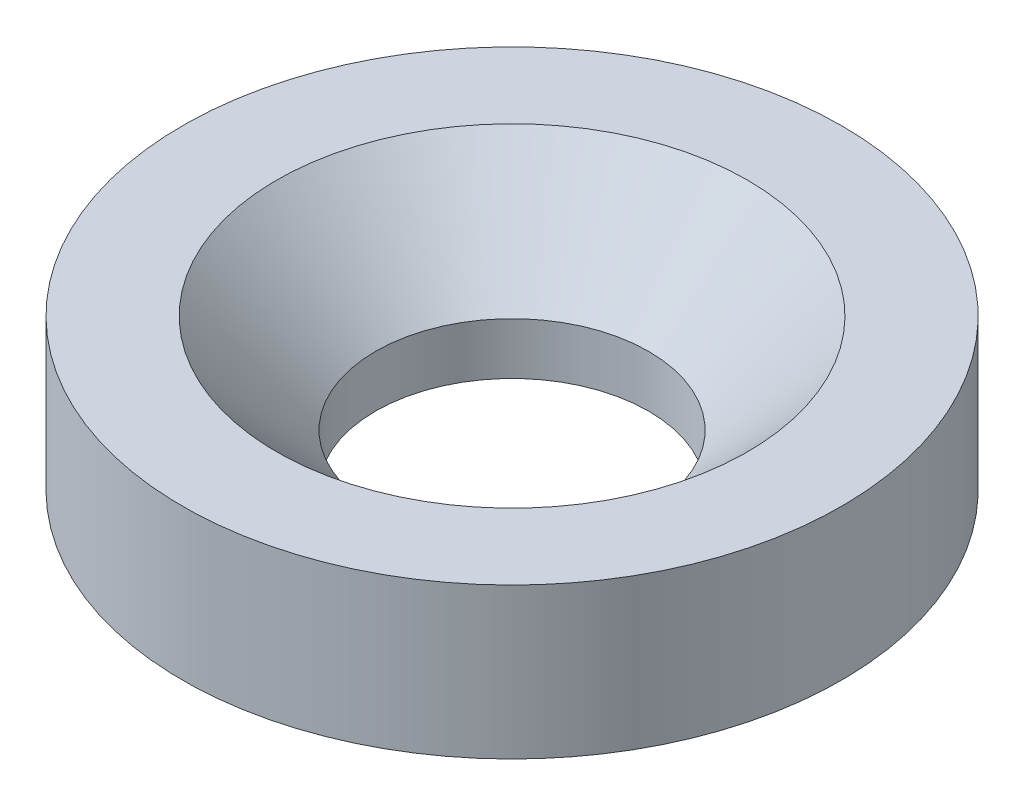
SolidWorks part; units mm, degrees
material "AISI 1020"
ref_plane "Front Plane" through (0, 0, 0) normal (0, 0, 1) x (1, 0, 0)
ref_plane "Top Plane" through (0, 0, 0) normal (0, 1, 0) x (1, 0, 0)
ref_plane "Right Plane" through (0, 0, 0) normal (1, 0, 0) x (0, 0, -1)
sketch "Sketch1" plane through (0, 0, 0) normal (0, 0, 1) x (1, 0, 0)
  line L0 (7.25, 0) -> (17.5, 0)
  line L1 (17.5, 0) -> (17.5, 8)
  line L2 (17.5, 8) -> (12.5, 8)
  line L3 (12.5, 8) -> (7.25, 2.75)
  line L4 (7.25, 2.75) -> (7.25, 0)
  line L5 (0, 0) -> (0, 6.3393) construction
  dimension "D1" = 17.5
  dimension "D2" = 7.25
  dimension "D3" = 12.5
  dimension "D4" = 8
  dimension "D5" = 45
revolve "Revolve1" add sketch "Sketch1" angle 360 about L5
